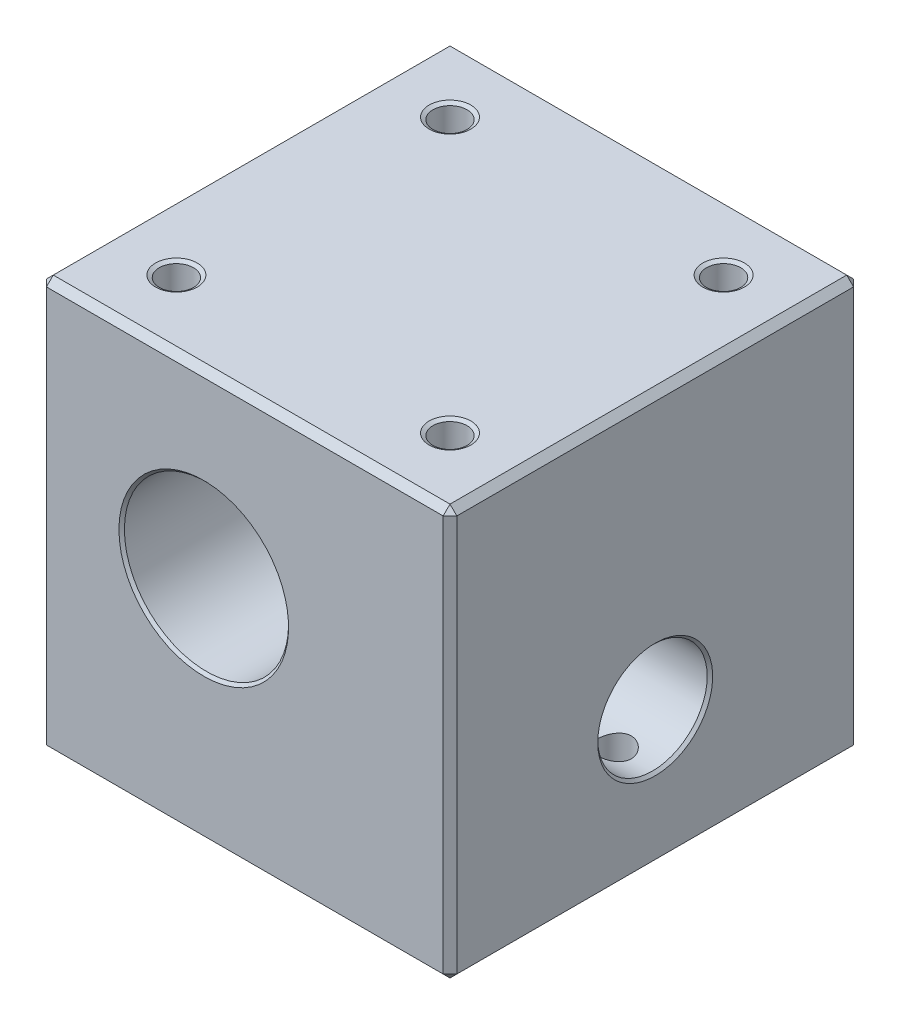
SolidWorks part; units mm, degrees
material "6063-T5"
ref_plane "Piano frontale" through (0, 0, 0) normal (0, 0, 1) x (1, 0, 0)
ref_plane "Piano superiore" through (0, 0, 0) normal (0, 1, 0) x (1, 0, 0)
ref_plane "Piano destro" through (0, 0, 0) normal (1, 0, 0) x (0, 0, -1)
sketch "Schizzo1" plane through (0, 0, 0) normal (0, 0, 1) x (1, 0, 0)
  line L0 (12, 6.5764) -> (12, 28.444) construction
  line L1 (0, 0) -> (30, 0)
  line L2 (0, 0) -> (0, 30)
  line L3 (0, 30) -> (30, 30)
  line L4 (30, 0) -> (30, 30)
  line L5 (6.315, 16.8) -> (24.6155, 16.8) construction
  circle A0 centre (12, 16.8) radius 6
  dimension "D3" = 12
  dimension "D1" = 30
  dimension "D2" = 30
  dimension "D4" = 12
  dimension "D5" = 13.2
extrude "Estrusione-Estrusione1" add sketch "Schizzo1" along normal blind 30
sketch "Schizzo3" plane through (30, 0, 0) normal (1, 0, 0) x (0, 0, -1)
  line L2 (-15, 10.16) -> (-15, 24.3684) construction
  line L3 (-30, 0) -> (-30, 30) construction
  line L4 (0, 0) -> (0, 30) construction
  line L5 (-30, 0) -> (0, 0) construction
  point P0 (-15, 10)
  dimension "D1" = 10
hole_wizard "Ø8.0 (8) Diameter Hole1" positions "Schizzo5" profile "Schizzo4" hole size "Ø8.0" standard "ISO"
sketch "Schizzo5" plane through (30, 0, 0) normal (1, 0, 0) x (0, 0, -1)
  point P0 (-15, 10)
sketch "Schizzo4" plane through (30, 10, 15) normal (0, 1, 0) x (0, 0, -1)
  line L0 (0, 0) -> (0, 15.9034)
  line L1 (0, 15.9034) -> (4, 13.5)
  line L2 (4, 13.5) -> (4, 0)
  line L5 (4, 0) -> (0, 0)
  line L10 (0, 15.9034) -> (-4, 13.5) construction
  line L11 (0, -6.35) -> (0, 107.95) construction
  dimension "Hole Dia." = 8
  dimension "Hole Depth" = 13.5
  dimension "Drill Angle" = 118
sketch "Schizzo6" plane through (0, 30, 0) normal (0, 1, 0) x (1, 0, 0)
  line L0 (-7.6843, -25) -> (41.504, -25) construction
  line L1 (0, -30) -> (0, 0) construction
  line L2 (30, -30) -> (0, -30) construction
  point P0 (5, -25)
  point P1 (25, -25)
  dimension "D1" = 20
  dimension "D2" = 5
  dimension "D3" = 5
hole_wizard "Foro filettato M3-1" positions "Schizzo8" profile "Schizzo7" tap size "M3" standard "ISO"
sketch "Schizzo8" plane through (0, 30, 0) normal (0, 1, 0) x (1, 0, 0)
  point P0 (5, -25)
  point P3 (25, -25)
sketch "Schizzo7" plane through (5, 30, 25) normal (1, 0, 0) x (0, 0, 1)
  line L0 (0, 0) -> (0, 9.2511)
  line L1 (0, 9.2511) -> (1.25, 8.5)
  line L2 (1.25, 8.5) -> (1.25, 0.1588)
  line L3 (1.25, 0.1588) -> (1.525, 0)
  line L5 (1.525, 0) -> (0, 0)
  line L6 (-1.25, 0.1588) -> (-1.525, 0) construction
  line L10 (0, 9.2511) -> (-1.25, 8.5) construction
  line L11 (0, -6.35) -> (0, 107.95) construction
  dimension "Tap Drill Dia." = 2.5
  dimension "Tap Drill Depth" = 8.5
  dimension "Near C'Sink Dia." = 3.05
  dimension "Near C'Sink Angle" = 120
  dimension "Drill Angle" = 118
cosmetic thread "Filettatura del foro1" parameters "D1"=6, "D2"=3
cosmetic thread "Filettatura del foro2" parameters "D1"=6, "D2"=3
ref_plane "Piano1" through (0, 0, 15) normal (0, 0, 1) x (1, 0, 0)
mirror "Specchia1" about plane through (0, 0, 15) normal (0, 0, 1) of "Foro filettato M3-1"
hole_wizard "Foro filettato M3-2" positions "Schizzo10" profile "Schizzo11" tap size "M3" standard "ISO"
sketch "Schizzo10" plane through (0, 0, 0) normal (0, -1, 0) x (-1, 0, 0)
  line L1 (-30, -30) -> (-30, 0) construction
  line L2 (-30, -15) -> (0, -15) construction
  line L3 (0, -30) -> (0, 0) construction
  point P0 (-27, -15)
  dimension "D2" = 3
sketch "Schizzo11" plane through (27, 0, 15) normal (1, 0, 0) x (0, 0, -1)
  line L0 (0, 0) -> (0, 9.2511)
  line L1 (0, 9.2511) -> (1.25, 8.5)
  line L2 (1.25, 8.5) -> (1.25, 0.1588)
  line L3 (1.25, 0.1588) -> (1.525, 0)
  line L5 (1.525, 0) -> (0, 0)
  line L6 (-1.25, 0.1588) -> (-1.525, 0) construction
  line L10 (0, 9.2511) -> (-1.25, 8.5) construction
  line L11 (0, -6.35) -> (0, 107.95) construction
  dimension "Tap Drill Dia." = 2.5
  dimension "Tap Drill Depth" = 8.5
  dimension "Near C'Sink Dia." = 3.05
  dimension "Near C'Sink Angle" = 120
  dimension "Drill Angle" = 118
chamfer "Chamfer1" distance 0.5 angle 45 12 edges at (30, 15, 0) (15, 0, 0) (0, 0, 15) (15, 0, 30) (30, 0, 15) (0, 15, 0) (0, 15, 30) (30, 15, 30) (15, 30, 0) (30, 30, 15) (0, 30, 15) (15, 30, 30)
chamfer "Chamfer2" distance 0.2 angle 45 3 edges at (18, 16.8, 0) (18, 16.8, 30) (30, 10, 11)
